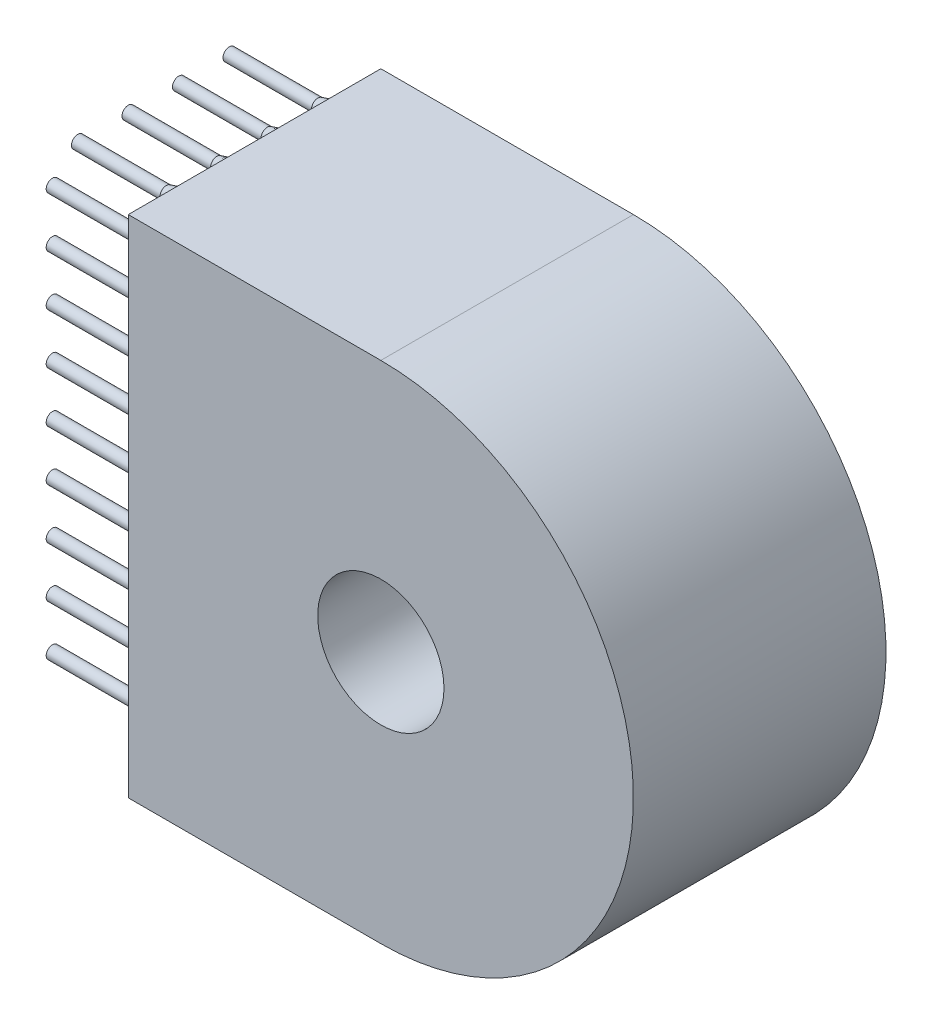
SolidWorks part; units mm, degrees
ref_plane "正面" through (0, 0, 0) normal (0, 0, 1) x (1, 0, 0)
ref_plane "平面" through (0, 0, 0) normal (0, 1, 0) x (1, 0, 0)
ref_plane "右側面" through (0, 0, 0) normal (1, 0, 0) x (0, 0, -1)
sketch "ｽｹｯﾁ1" plane through (0, 0, 0) normal (0, 0, 1) x (1, 0, 0)
  line L0 (0, 10) -> (-10, 10)
  line L1 (-10, 10) -> (-10, -10)
  line L2 (-10, -10) -> (0, -10)
  circle A0 centre (0, 0) radius 2.5
  arc A1 (0, -10) -> (0, 10) centre (0, 0) ccw
  dimension "D1" = 5
  dimension "D2" = 20
extrude "ﾎﾞｽ - 押し出し1" add sketch "ｽｹｯﾁ1" along normal blind 10
sketch "ｽｹｯﾁ2" plane through (-10, 0, 0) normal (-1, 0, 0) x (0, 0, 1)
  line L0 (10, 10) -> (0, 10) construction
  line L1 (0, 10) -> (0, -10) construction
  circle A0 centre (1, 8.5) radius 0.25
  circle A1 centre (2, 7.5) radius 0.25
  dimension "D1" = 0.5
  dimension "D2" = 1.5
  dimension "D3" = 1
  dimension "D4" = 0.5
  dimension "D5" = 1
  dimension "D6" = 1
extrude "ﾎﾞｽ - 押し出し2" add sketch "ｽｹｯﾁ2" along normal blind 5
chamfer "面取り1" distance 0.4 angle 75 2 edges at (-10, 8.5, 0.75) (-10, 7.5, 1.75)
pattern_linear "直線ﾊﾟﾀｰﾝ1" count 4 spacing 2 along (0, 0, 1) count 9 spacing 2 along (0, -1, 0) of "ﾎﾞｽ - 押し出し2", "面取り1"
